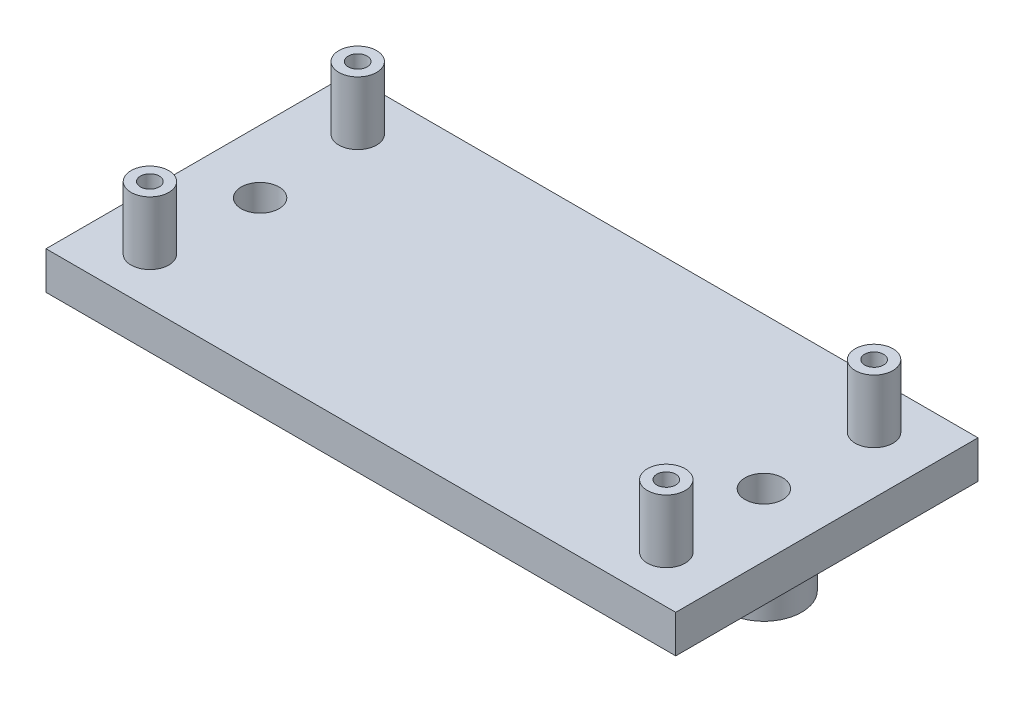
SolidWorks part; units mm, degrees
ref_plane "Front Plane" through (0, 0, 0) normal (0, 0, 1) x (1, 0, 0)
ref_plane "Top Plane" through (0, 0, 0) normal (0, 1, 0) x (1, 0, 0)
ref_plane "Right Plane" through (0, 0, 0) normal (1, 0, 0) x (0, 0, -1)
sketch "Sketch1" plane through (0, 0, 0) normal (0, 1, 0) x (1, 0, 0)
  line L1 (0, 0) -> (50, 0)
  line L2 (0, 0) -> (0, -24)
  line L3 (0, -24) -> (50, -24)
  line L4 (50, 0) -> (50, -24)
  dimension "D1" = 24
  dimension "D2" = 50
extrude "Boss-Extrude1" add sketch "Sketch1" along normal blind 3
sketch "Sketch2" plane through (0, 0, 0) normal (0, -1, 0) x (1, 0, 0)
  line L0 (25, 24) -> (25, 0) construction
  line L1 (0, 24) -> (50, 24) construction
  line L2 (50, 0) -> (0, 0) construction
  line L3 (25, 12) -> (5, 12) construction
  circle A0 centre (5, 12) radius 1.5
  circle A1 centre (5, 12) radius 3
  circle A2 centre (45, 12) radius 3
  circle A3 centre (45, 12) radius 1.5
  dimension "D1" = 3
  dimension "D2" = 6
  dimension "D3" = 20
extrude "Boss-Extrude2" add sketch "Sketch2" along normal blind 4
sketch "Sketch3" plane through (0, 3, 0) normal (0, 1, 0) x (1, 0, 0)
  line L0 (25, 0) -> (25, -24) construction
  line L1 (50, 0) -> (0, 0) construction
  line L2 (0, -24) -> (50, -24) construction
  line L4 (4.5, -20.25) -> (45.5, -20.25) construction
  line L5 (4.5, -20.25) -> (4.5, -3.75) construction
  line L6 (4.5, -3.75) -> (45.5, -3.75) construction
  line L7 (45.5, -20.25) -> (45.5, -3.75) construction
  line L8 (4.5, -20.25) -> (45.5, -3.75) construction
  line L9 (4.5, -3.75) -> (45.5, -20.25) construction
  circle A0 centre (4.5, -3.75) radius 0.9
  circle A1 centre (45.5, -3.75) radius 0.9
  circle A2 centre (45.5, -20.25) radius 0.9
  circle A3 centre (4.5, -20.25) radius 0.9
  point P6 (25, -12)
  dimension "D3" = 1.8
  dimension "D4" = 1.8
  dimension "D5" = 1.8
  dimension "D6" = 1.8
  dimension "D1" = 16.5
  dimension "D2" = 41
extrude "Cut-Extrude1" cut sketch "Sketch3" against normal blind 10
sketch "Sketch4" plane through (0, 3, 0) normal (0, 1, 0) x (1, 0, 0)
  circle A0 centre (4.5, -3.75) radius 1.5
  circle A1 centre (45.5, -3.75) radius 1.5
  circle A2 centre (4.5, -20.25) radius 1.5
  circle A3 centre (45.5, -20.25) radius 1.5
  circle A4 centre (45.5, -20.25) radius 0.75
  circle A5 centre (45.5, -3.75) radius 0.75
  circle A6 centre (4.5, -3.75) radius 0.75
  circle A7 centre (4.5, -20.25) radius 0.75
  dimension "D1" = 3
  dimension "D2" = 3
  dimension "D3" = 3
  dimension "D4" = 3
  dimension "D5" = 1.5
  dimension "D6" = 1.5
  dimension "D7" = 1.5
  dimension "D8" = 1.5
extrude "Boss-Extrude3" add sketch "Sketch4" along normal blind 5
sketch "Sketch5" plane through (0, 0, 0) normal (0, -1, 0) x (1, 0, 0)
  circle A0 centre (5, 12) radius 1.5
  circle A1 centre (45, 12) radius 1.5
  dimension "D1" = 3
  dimension "D2" = 3
extrude "Cut-Extrude2" cut sketch "Sketch5" against normal blind 10
